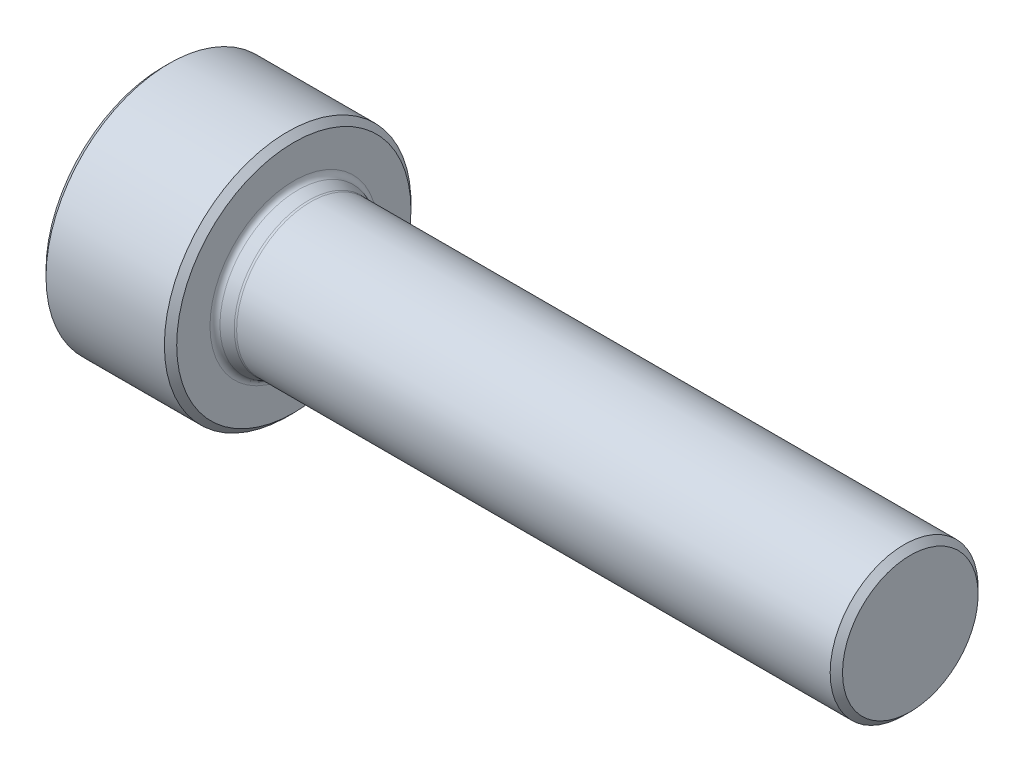
SolidWorks part; units mm, degrees
material "AISI 1020"
ref_plane "Спереди" through (0, 0, 0) normal (0, 0, 1) x (1, 0, 0)
ref_plane "Сверху" through (0, 0, 0) normal (0, 1, 0) x (1, 0, 0)
ref_plane "Справа" through (0, 0, 0) normal (1, 0, 0) x (0, 0, -1)
sketch "Эскиз1" plane through (0, 0, 0) normal (0, 0, 1) x (1, 0, 0)
  line L0 (-1000, 0) -> (49000, 0) construction
  line L1 (-4.9825, 2.5) -> (-5.3, 3.05)
  line L2 (-5.3, 3.05) -> (-5.3, 5)
  line L3 (-5.3, 5) -> (0, 5)
  line L4 (0, 5) -> (0, 3.4)
  line L5 (0.1677, 3.1639) -> (0.5977, 3.0139)
  line L6 (0.68, 3) -> (25, 3)
  line L7 (25, 3) -> (25, 0)
  line L8 (-4.9825, 2.5) -> (-2.3, 2.5)
  line L9 (-2.3, 2.5) -> (-0.8566, 0)
  line L10 (25, 0) -> (-0.8566, 0)
  arc A0 (0.5977, 3.0139) -> (0.68, 3) centre (0.68, 3.25) ccw
  arc A1 (0, 3.4) -> (0.1677, 3.1639) centre (0.25, 3.4) ccw
  dimension "c" = 0.25
  dimension "UGOL" = 60
  dimension "D" = 10
  dimension "t" = 3
  dimension "w" = 2.3
  dimension "l" = 25
  dimension "D_1" = 6.1
  dimension "S" = 5
  dimension "da" = 6.8
  dimension "f" = 0.68
  dimension "_d" = 6
revolve "Повернуть1" add sketch "Эскиз1" angle 360 about L0
sketch "Эскиз2" plane through (-5.3, 0, 0) normal (-1, 0, 0) x (0, 0, 1)
  line L1 (-0.0381, 2.8647) -> (-2.4619, 1.4654)
  line L2 (-2.5, 1.3994) -> (-2.5, -1.3994)
  line L3 (-2.4619, -1.4654) -> (-0.0381, -2.8647)
  line L4 (0.0381, -2.8647) -> (2.4619, -1.4654)
  line L5 (2.5, -1.3994) -> (2.5, 1.3994)
  line L6 (2.4619, 1.4654) -> (0.0381, 2.8647)
  arc A1 (2.4619, -1.4654) -> (2.5, -1.3994) centre (0, 0) ccw
  arc A2 (2.5, 1.3994) -> (2.4619, 1.4654) centre (0, 0) ccw
  arc A3 (0.0381, 2.8647) -> (-0.0381, 2.8647) centre (0, 0) ccw
  arc A4 (-2.4619, 1.4654) -> (-2.5, 1.3994) centre (0, 0) ccw
  arc A5 (-2.5, -1.3994) -> (-2.4619, -1.4654) centre (0, 0) ccw
  arc A6 (-0.0381, -2.8647) -> (0.0381, -2.8647) centre (0, 0) ccw
  dimension "e" = 5.73
  dimension "S" = 5
  dimension "UG1" = 120
  dimension "UG2" = 120
extrude "Вырез-Вытянуть1" cut sketch "Эскиз2" against normal blind 3
chamfer "Фаска1" distance 0.25 3 edges at (0, 0, 5) (-5.3, 0, 5) (25, 0, 3)
equation "\"t@Вырез-Вытянуть1\"=1.3"
